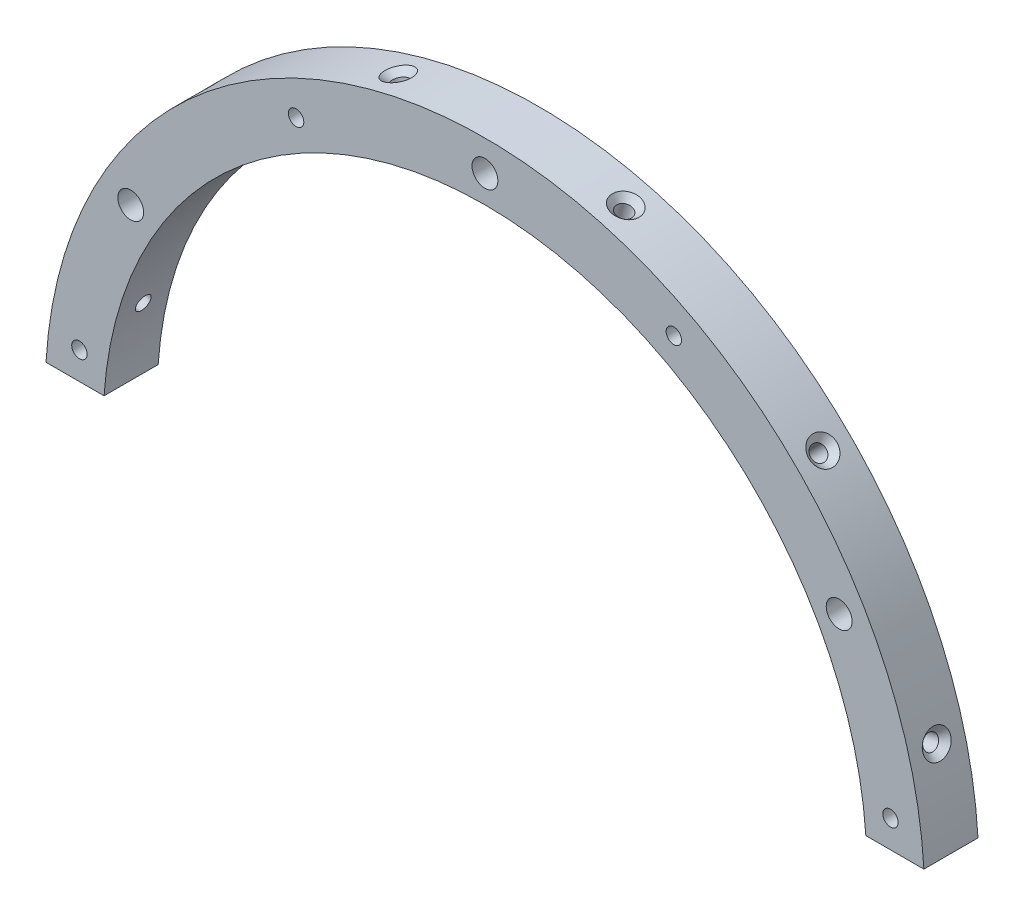
SolidWorks part; units mm, degrees
material "6061-T6 (SS)"
ref_plane "Front Plane" through (0, 0, 0) normal (0, 0, 1) x (1, 0, 0)
ref_plane "Top Plane" through (0, 0, 0) normal (0, 1, 0) x (1, 0, 0)
ref_plane "Right Plane" through (0, 0, 0) normal (1, 0, 0) x (0, 0, -1)
sketch "Sketch1" plane through (0, 0, 0) normal (0, 0, 1) x (1, 0, 0)
  line L0 (0, 0) -> (0, 44.9951) construction
  line L1 (0, 0) -> (-45.769, 0) construction
  line L2 (-64.388, 3.8) -> (-55.8709, 3.8)
  line L3 (64.388, 3.8) -> (55.8709, 3.8)
  arc A0 (64.388, 3.8) -> (-64.388, 3.8) centre (0, 0) ccw
  arc A1 (55.8709, 3.8) -> (-55.8709, 3.8) centre (0, 0) ccw
  dimension "D2" = 64.5
  dimension "D3" = 56
  dimension "D1" = 3.8
extrude "Boss-Extrude1" add sketch "Sketch1" along normal mid plane 7.9375
sketch "Sketch2" plane through (0, 0, 0) normal (0, 0, 1) x (1, 0, 0)
  line L0 (0, 0) -> (63.2441, 16.9462)
  line L1 (0, 0) -> (104.4949, 0) construction
  dimension "D1" = 15
hole_wizard "#4-40 Tapped Hole2" positions "3DSketch1" profile "Sketch3" tap size "#4-40" standard "ANSI Inch"
sketch3d "3DSketch1"
  line L0 (0, 0, 0) -> (63.2441, 16.9462, 0) construction
  point P0 (62.3022, 16.6938, 0)
sketch "Sketch3" plane through (62.3022, 16.6938, 0) normal (0, 0, 1) x (-0.2588, 0.9659, 0)
  line L0 (0, 0) -> (0, 9.5492)
  line L1 (0, 9.5492) -> (1.1303, 8.87)
  line L2 (1.1303, 8.87) -> (1.1303, 0.9271)
  line L3 (1.1303, 0.9271) -> (2.0574, 0)
  line L5 (2.0574, 0) -> (0, 0)
  line L6 (-1.1303, 0.9271) -> (-2.0574, 0) construction
  line L10 (0, 9.5492) -> (-1.1303, 8.87) construction
  line L11 (0, -6.35) -> (0, 107.95) construction
  dimension "Tap Drill Dia." = 2.2606
  dimension "Tap Drill Depth" = 8.87
  dimension "Near C'Sink Dia." = 4.1148
  dimension "Near C'Sink Angle" = 90
  dimension "Drill Angle" = 118
cosmetic thread "Hole Thread1" parameters "D1"=5.69, "D2"=2.8448
pattern_circular "CirPattern1" count 6 every 30 about axis through (0, 0, 3.9688) along (0, 0, -1) of "#4-40 Tapped Hole2"
hole_wizard "#4-40 Tapped Hole3" positions "Sketch5" profile "Sketch4" tap size "#4-40" standard "ANSI Inch" end condition through all
sketch "Sketch5" plane through (0, 0, -3.9688) normal (0, 0, -1) x (-1, 0, 0)
  line L0 (0, 0) -> (-34.4115, 0) construction
  line L1 (0, 0) -> (-33.5444, 4.4162) construction
  point P0 (-59.4867, 7.8316)
  dimension "D1" = 7.5
  dimension "D2" = 60
sketch "Sketch4" plane through (59.4867, 7.8316, -3.9688) normal (1, 0, 0) x (0, 1, 0)
  line L0 (0, 0) -> (0, 7.9375)
  line L1 (0, 7.9375) -> (1.1303, 7.9375)
  line L2 (1.1303, 7.9375) -> (1.1303, 0.9271)
  line L3 (1.1303, 0.9271) -> (2.0574, 0)
  line L5 (2.0574, 0) -> (0, 0)
  line L6 (-1.1303, 0.9271) -> (-2.0574, 0) construction
  line L11 (0, -6.35) -> (0, 107.95) construction
  dimension "Thru Tap Drill Dia." = 2.2606
  dimension "Thru Tap Drill Depth" = 7.9375
  dimension "Near C'Sink Dia." = 4.1148
  dimension "Near C'Sink Angle" = 90
cosmetic thread "Hole Thread2" parameters "D2"=2.8448
pattern_circular "CirPattern2" count 4 every 55 about axis through (0, 0, 0) along (0, 0, 1) of "#4-40 Tapped Hole3"
hole_wizard "#10-24 Tapped Hole1" positions "Sketch7" profile "Sketch6" tap size "#10-24" standard "ANSI Inch" end condition through all
sketch "Sketch7" plane through (0, 0, -3.9688) normal (0, 0, -1) x (-1, 0, 0)
  line L0 (0, 0) -> (-39.3914, 0) construction
  line L1 (0, 0) -> (-31.494, 18.183) construction
  point P0 (-51.9615, 30)
  dimension "D1" = 30
  dimension "D2" = 60
sketch "Sketch6" plane through (51.9615, 30, -3.9688) normal (1, 0, 0) x (0, 1, 0)
  line L0 (0, 0) -> (0, 7.9375)
  line L1 (0, 7.9375) -> (1.8986, 7.9375)
  line L2 (1.8986, 7.9375) -> (1.8986, 1.1494)
  line L3 (1.8986, 1.1494) -> (3.048, 0)
  line L5 (3.048, 0) -> (0, 0)
  line L6 (-1.8986, 1.1494) -> (-3.048, 0) construction
  line L11 (0, -6.35) -> (0, 107.95) construction
  dimension "Thru Tap Drill Dia." = 3.7973
  dimension "Thru Tap Drill Depth" = 7.9375
  dimension "Near C'Sink Dia." = 6.096
  dimension "Near C'Sink Angle" = 90
cosmetic thread "Hole Thread3" parameters "D2"=4.826
pattern_circular "CirPattern3" count 3 every 60 about axis through (0, 0, 0) along (0, 0, 1) of "#10-24 Tapped Hole1"
